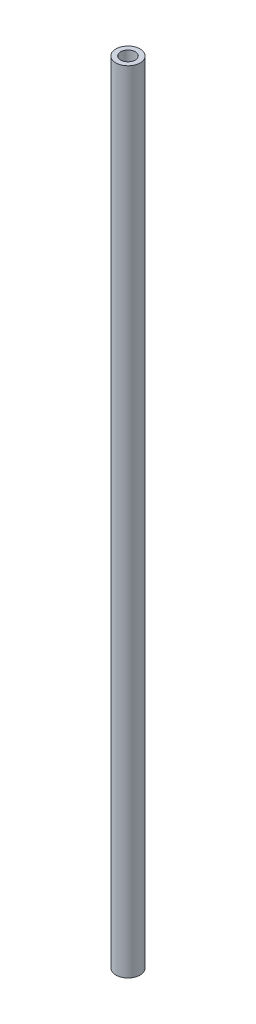
SolidWorks part; units mm, degrees
material "Thornel VCB-20 Carbon Cloth"
ref_plane "Front Plane" through (0, 0, 0) normal (0, 0, 1) x (1, 0, 0)
ref_plane "Top Plane" through (0, 0, 0) normal (0, 1, 0) x (1, 0, 0)
ref_plane "Right Plane" through (0, 0, 0) normal (1, 0, 0) x (0, 0, -1)
sketch "Sketch2" plane through (0, 0, 0) normal (0, 1, 0) x (1, 0, 0)
  circle A0 centre (0, 0) radius 2.5
  circle A1 centre (0, 0) radius 1.5
  dimension "D1" = 5
  dimension "D2" = 3
extrude "Boss-Extrude3" add sketch "Sketch2" along normal mid plane 163 contours A1 | A0
